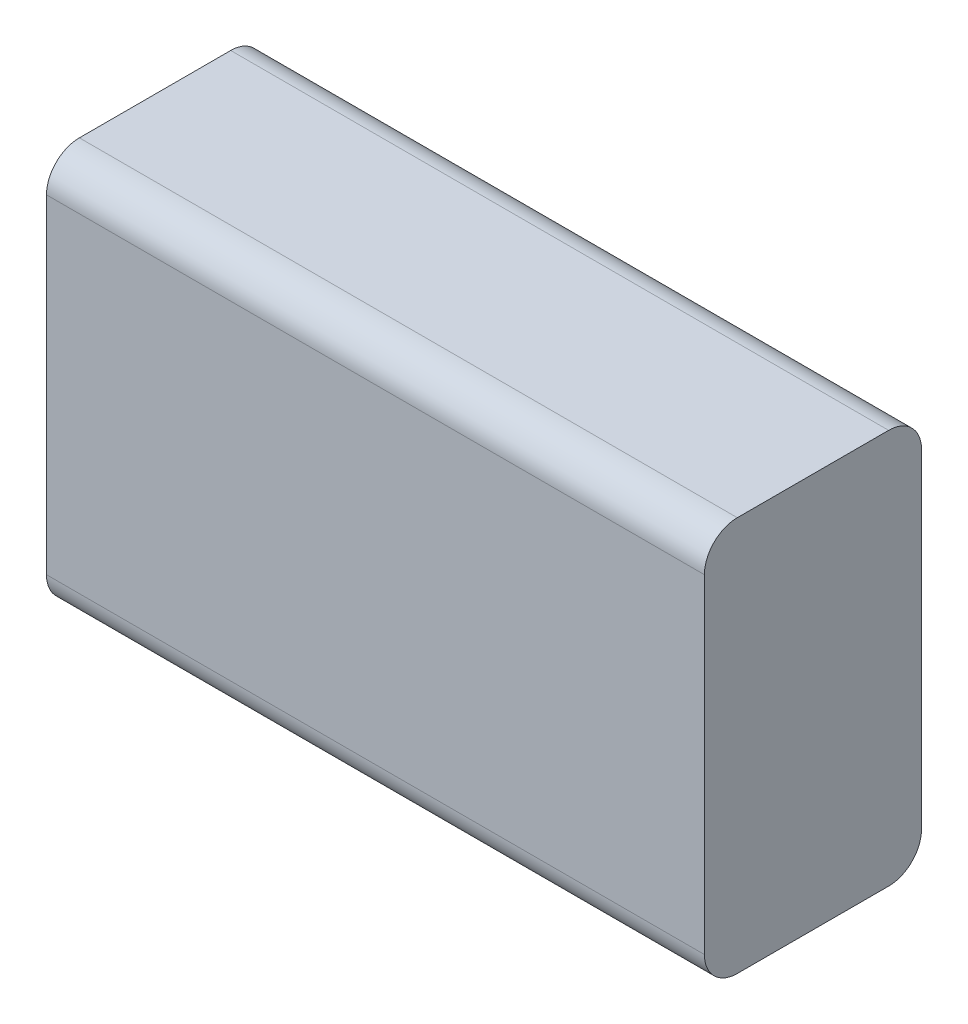
SolidWorks part; units mm, degrees
ref_plane "Front Plane" through (0, 0, 0) normal (0, 0, 1) x (1, 0, 0)
ref_plane "Top Plane" through (0, 0, 0) normal (0, 1, 0) x (1, 0, 0)
ref_plane "Right Plane" through (0, 0, 0) normal (1, 0, 0) x (0, 0, -1)
sketch "Sketch1" plane through (0, 0, 0) normal (0, 1, 0) x (1, 0, 0)
  line L1 (0, 0) -> (1, 0)
  line L2 (0, 0) -> (0, -0.33)
  line L3 (0, -0.33) -> (1, -0.33)
  line L4 (1, 0) -> (1, -0.33)
  dimension "D1" = 1
  dimension "D2" = 0.33
extrude "Boss-Extrude1" add sketch "Sketch1" along normal blind 0.6
fillet "Fillet2" radius 0.05 4 edges at (0.5, 0.6, 0.33) (0.5, 0, 0.33) (0.5, 0, 0) (0.5, 0.6, 0)
sketch "Sketch2" plane through (0, 0, 0) normal (0, 0, -1) x (-1, 0, 0)
  line L0 (-0.5, 0.05) -> (-0.5, 0.55) construction
  line L1 (0, 0.55) -> (-1, 0.55) construction
  line L2 (-1, 0.05) -> (0, 0.05) construction
  point P4 (-0.5, 0.55)
  point P7 (-0.5, 0.05)
sketch "Sketch3" plane through (0, 0, 0) normal (-1, 0, 0) x (0, 0, 1)
  line L0 (0, 0.55) -> (0, 0.05) construction
  line L1 (0.05, 0.6) -> (0.28, 0.6) construction
  circle A0 centre (0.165, 0.3) radius 0.05 construction
  point P4 (0, 0.3)
  point P7 (0.165, 0.6)
  dimension "D1" = 0.1
